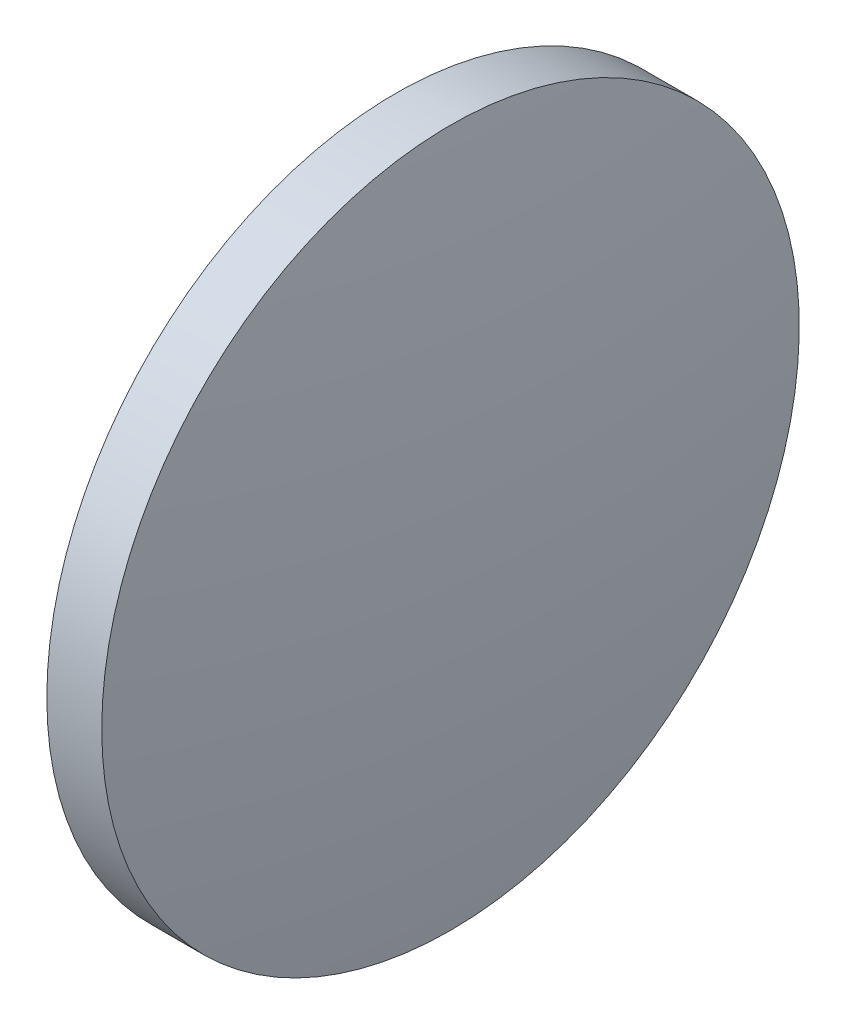
SolidWorks part; units mm, degrees
ref_plane "前视基准面" through (0, 0, 0) normal (0, 0, 1) x (1, 0, 0)
ref_plane "上视基准面" through (0, 0, 0) normal (0, 1, 0) x (1, 0, 0)
ref_plane "右视基准面" through (0, 0, 0) normal (1, 0, 0) x (0, 0, -1)
sketch "草图1" plane through (0, 0, 0) normal (0, 0, 1) x (1, 0, 0)
  line L0 (429.7994, 72.769) -> (448.5954, 72.769) construction
  line L1 (435.5041, 72.769) -> (435.5041, 85.469)
  line L2 (435.5041, 85.469) -> (437.5041, 85.469)
  line L3 (438.3941, 72.769) -> (435.5041, 72.769)
  arc A0 (438.3941, 72.769) -> (437.5041, 85.469) centre (347.3402, 72.769) ccw
revolve "旋转1" add sketch "草图1" angle 360 about L0
